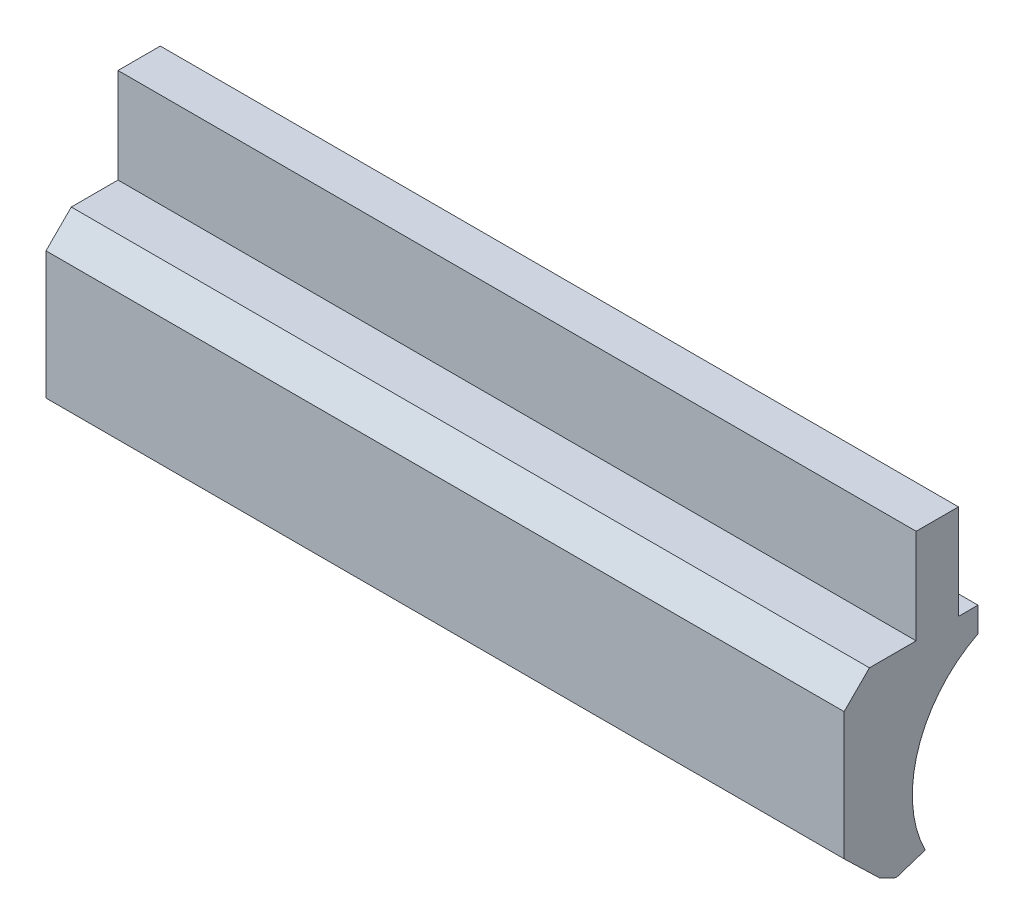
SolidWorks part; units mm, degrees
ref_plane "Front Plane" through (0, 0, 0) normal (0, 0, 1) x (1, 0, 0)
ref_plane "Top Plane" through (0, 0, 0) normal (0, 1, 0) x (1, 0, 0)
ref_plane "Right Plane" through (0, 0, 0) normal (1, 0, 0) x (0, 0, -1)
sketch "Sketch1" plane through (0, 0, 0) normal (1, 0, 0) x (0, 0, -1)
  line L0 (0.1815, 0.2015) -> (-0.3485, 0.2015)
  line L1 (-0.3485, 0.2015) -> (-0.3485, -0.9874)
  line L2 (-0.3485, -0.9874) -> (-0.9338, -0.9874)
  line L3 (-0.9338, -0.9874) -> (-1.2506, -1.3043)
  line L4 (-1.2506, -1.3043) -> (-1.2506, -2.9024)
  line L5 (-1.2506, -2.9024) -> (-0.8064, -3.3313)
  line L6 (-0.8064, -3.3313) -> (-0.5988, -3.4326)
  line L7 (-0.5988, -3.4326) -> (-0.2349, -3.3144)
  line L9 (0.1815, 0.2015) -> (0.1815, -0.9874)
  line L11 (0.4264, -1.2988) -> (0.4264, -0.9874)
  line L12 (0.4264, -0.9874) -> (0.1815, -0.9874)
  arc A1 (-0.2349, -3.3144) -> (0.4264, -1.2988) centre (1.1036, -2.6372) cw
  dimension "D1" = 0.53
  dimension "D2" = 135
  dimension "D3" = 134
  dimension "D4" = 162
  dimension "D5" = 44
extrude "Boss-Extrude2" add sketch "Sketch1" along normal blind 10
